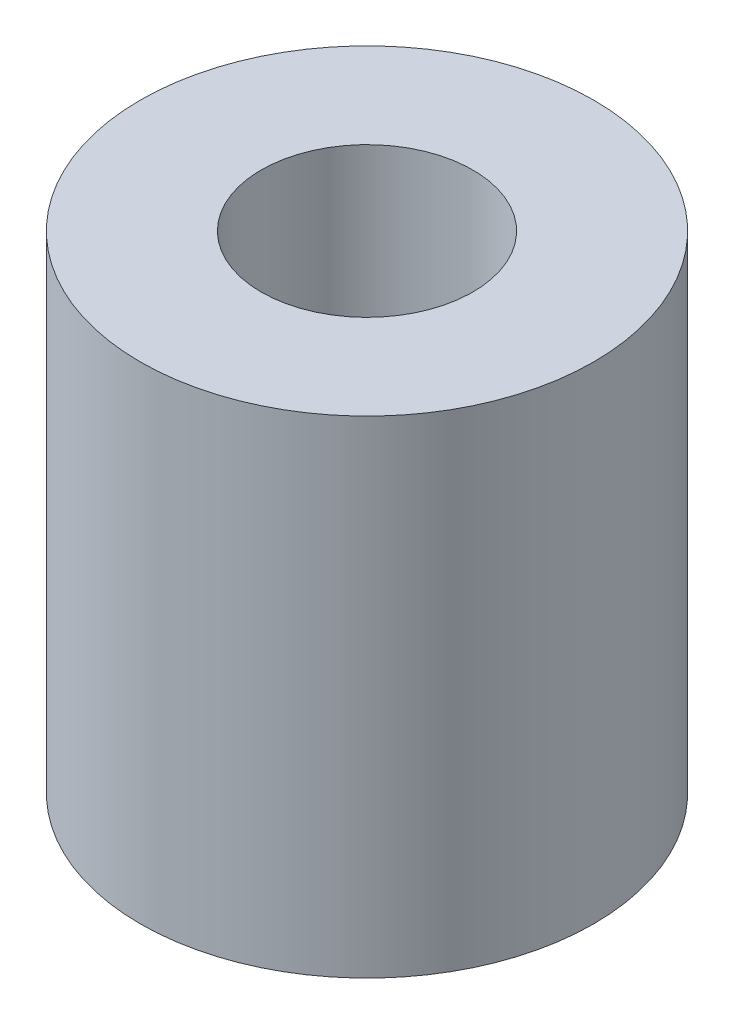
SolidWorks part; units mm, degrees
ref_plane "Front Plane" through (0, 0, 0) normal (0, 0, 1) x (1, 0, 0)
ref_plane "Top Plane" through (0, 0, 0) normal (0, 1, 0) x (1, 0, 0)
ref_plane "Right Plane" through (0, 0, 0) normal (1, 0, 0) x (0, 0, -1)
sketch "Sketch1" plane through (0, 0, 0) normal (0, 1, 0) x (1, 0, 0)
  circle A0 centre (0, 0) radius 3.75
  circle A1 centre (0, 0) radius 1.75
  dimension "D1" = 3.5
  dimension "D2" = 7.5
extrude "Boss-Extrude1" add sketch "Sketch1" along normal blind 8.05
